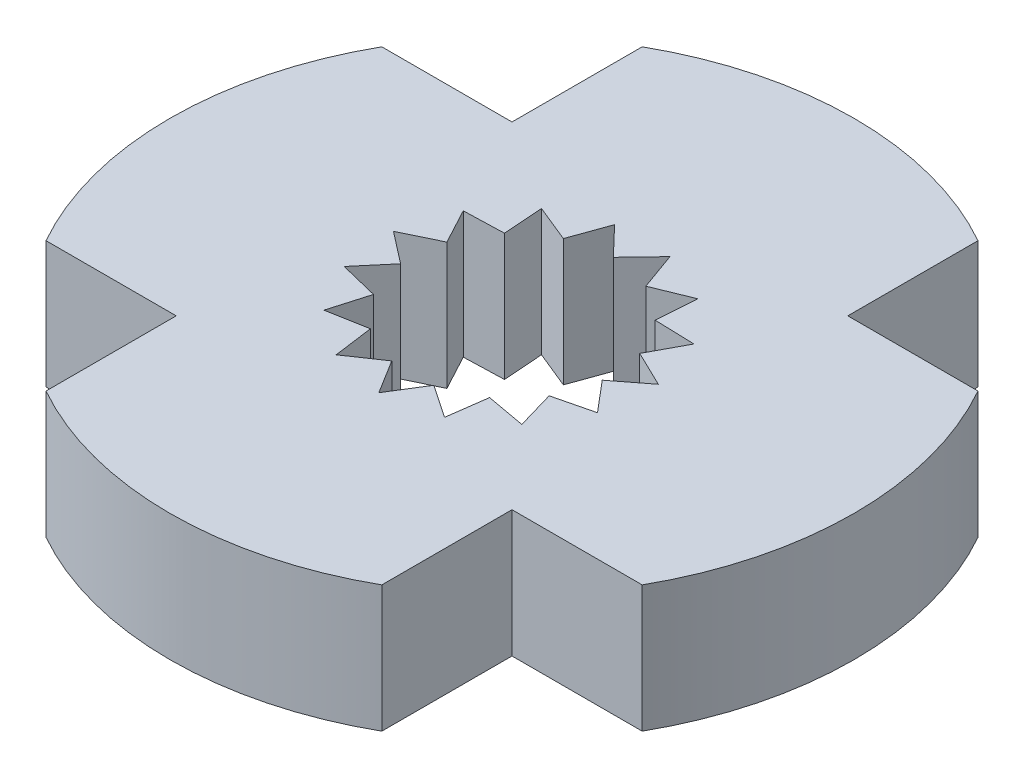
SolidWorks part; units mm, degrees
ref_plane "正面" through (0, 0, 0) normal (0, 0, 1) x (1, 0, 0)
ref_plane "平面" through (0, 0, 0) normal (0, 1, 0) x (1, 0, 0)
ref_plane "右側面" through (0, 0, 0) normal (1, 0, 0) x (0, 0, -1)
sketch "ｽｹｯﾁ1" plane through (0, 0, 0) normal (0, 1, 0) x (1, 0, 0)
  line L30 (0, 1.6) -> (0.437, 2.056) construction
  line L31 (0.6508, 1.4617) -> (1.2355, 1.7005) construction
  line L32 (0.6508, 1.4617) -> (0.437, 2.056) construction
  line L33 (1.189, 1.0706) -> (1.8203, 1.051) construction
  line L34 (1.189, 1.0706) -> (1.2355, 1.7005) construction
  line L35 (1.5217, 0.4944) -> (2.0904, 0.2197) construction
  line L36 (1.5217, 0.4944) -> (1.8203, 1.051) construction
  line L37 (1.5912, -0.1672) -> (1.9991, -0.6495) construction
  line L38 (1.5912, -0.1672) -> (2.0904, 0.2197) construction
  line L39 (1.3856, -0.8) -> (1.562, -1.4065) construction
  line L40 (1.3856, -0.8) -> (1.9991, -0.6495) construction
  line L41 (0.9405, -1.2944) -> (0.8549, -1.9202) construction
  line L42 (0.9405, -1.2944) -> (1.562, -1.4065) construction
  line L43 (0.3327, -1.565) -> (0, -2.1019) construction
  line L44 (0.3327, -1.565) -> (0.8549, -1.9202) construction
  line L45 (-0.3327, -1.565) -> (-0.8549, -1.9202) construction
  line L46 (-0.3327, -1.565) -> (0, -2.1019) construction
  line L47 (-0.9405, -1.2944) -> (-1.562, -1.4065) construction
  line L48 (-0.9405, -1.2944) -> (-0.8549, -1.9202) construction
  line L49 (-1.3856, -0.8) -> (-1.9991, -0.6495) construction
  line L50 (-1.3856, -0.8) -> (-1.562, -1.4065) construction
  line L51 (-1.5912, -0.1672) -> (-2.0904, 0.2197) construction
  line L52 (-1.5912, -0.1672) -> (-1.9991, -0.6495) construction
  line L53 (-1.5217, 0.4944) -> (-1.8203, 1.051) construction
  line L54 (-1.5217, 0.4944) -> (-2.0904, 0.2197) construction
  line L55 (-1.189, 1.0706) -> (-1.2355, 1.7005) construction
  line L56 (-1.189, 1.0706) -> (-1.8203, 1.051) construction
  line L57 (-0.6508, 1.4617) -> (-0.437, 2.056) construction
  line L58 (-0.6508, 1.4617) -> (-1.2355, 1.7005) construction
  line L59 (0, 1.6) -> (-0.437, 2.056) construction
  line L60 (2.65, 4.7051) -> (2.65, 2.65)
  line L61 (-2.65, 4.7051) -> (-2.65, 2.65)
  line L63 (-4.7051, 2.65) -> (-2.65, 2.65)
  line L64 (-4.7051, -2.65) -> (-2.65, -2.65)
  line L65 (-2.65, -2.65) -> (-2.65, -4.7051)
  line L66 (2.65, -2.65) -> (2.65, -4.7051)
  line L67 (2.65, 2.65) -> (4.7051, 2.65)
  line L68 (2.65, -2.65) -> (4.7051, -2.65)
  arc A2 (-4.7051, 2.65) -> (-4.7051, -2.65) centre (0, 0) ccw
  arc A3 (2.65, 4.7051) -> (-2.65, 4.7051) centre (0, 0) ccw
  arc A4 (4.7051, -2.65) -> (4.7051, 2.65) centre (0, 0) ccw
  arc A5 (-2.65, -4.7051) -> (2.65, -4.7051) centre (0, 0) ccw
extrude "ﾎﾞｽ - 押し出し1" add sketch "ｽｹｯﾁ1" along normal blind 2
sketch "ｽｹｯﾁ2" plane through (0, 0, 0) normal (0, -1, 0) x (1, 0, 0)
  circle A0 centre (0, 0) radius 2.575
  circle A1 centre (0, 0) radius 0.85
  dimension "D1" = 5.15
  dimension "D2" = 1.7
extrude "ﾎﾞｽ - 押し出し2" [suppressed] add sketch "ｽｹｯﾁ2" along normal blind 1.5
sketch "ｽｹｯﾁ3" [suppressed] plane through (0, -1.5, 0) normal (0, -1, 0) x (1, 0, 0)
  circle A0 centre (0, 0) radius 1.55
  dimension "D1" = 3.1
extrude "ｶｯﾄ - 押し出し1" [suppressed] cut sketch "ｽｹｯﾁ3" against normal blind 0.3
sketch "ｽｹｯﾁ4" plane through (0, 2, 0) normal (0, 1, 0) x (1, 0, 0)
  line L0 (0, 0) -> (0, 2.4324) construction
  line L1 (0, 0) -> (0.5057, 2.3792) construction
  line L2 (0, 0) -> (0.9893, 2.2221) construction
  line L3 (0, 0) -> (1.4297, 1.9678) construction
  line L4 (0, 0) -> (1.8076, 1.6276) construction
  line L5 (0, 0) -> (2.1065, 1.2162) construction
  line L6 (0, 0) -> (2.3133, 0.7516) construction
  line L7 (0, 0) -> (2.419, 0.2543) construction
  line L24 (0, 0) -> (2.419, -0.2543) construction
  line L25 (0, 0) -> (2.3133, -0.7516) construction
  line L26 (0, 0) -> (2.1065, -1.2162) construction
  line L27 (0, 0) -> (1.8076, -1.6276) construction
  line L28 (0, 0) -> (1.4297, -1.9678) construction
  line L29 (0, 0) -> (0.9893, -2.2221) construction
  line L30 (0, 0) -> (0.5057, -2.3792) construction
  line L31 (0, 0) -> (0, -2.4324) construction
  line L32 (0, 0) -> (-0.5057, -2.3792) construction
  line L33 (0, 0) -> (-0.9893, -2.2221) construction
  line L34 (0, 0) -> (-1.4297, -1.9678) construction
  line L35 (0, 0) -> (-1.8076, -1.6276) construction
  line L36 (0, 0) -> (-2.1065, -1.2162) construction
  line L37 (0, 0) -> (-2.3133, -0.7516) construction
  line L38 (0, 0) -> (-2.419, -0.2543) construction
  line L39 (0, 0) -> (-2.419, 0.2543) construction
  line L40 (0, 0) -> (-2.3133, 0.7516) construction
  line L41 (0, 0) -> (-2.1065, 1.2162) construction
  line L42 (0, 0) -> (-1.8076, 1.6276) construction
  line L43 (0, 0) -> (-1.4297, 1.9678) construction
  line L44 (0, 0) -> (-0.9893, 2.2221) construction
  line L45 (0, 0) -> (-0.5057, 2.3792) construction
  line L46 (0, 1.6) -> (0.437, 2.056)
  line L47 (0.6508, 1.4617) -> (1.2355, 1.7005)
  line L48 (0.6508, 1.4617) -> (0.437, 2.056)
  line L49 (1.189, 1.0706) -> (1.8203, 1.051)
  line L50 (1.189, 1.0706) -> (1.2355, 1.7005)
  line L51 (1.5217, 0.4944) -> (2.0904, 0.2197)
  line L52 (1.5217, 0.4944) -> (1.8203, 1.051)
  line L53 (1.5912, -0.1672) -> (1.9991, -0.6495)
  line L54 (1.5912, -0.1672) -> (2.0904, 0.2197)
  line L55 (1.3856, -0.8) -> (1.562, -1.4065)
  line L56 (1.3856, -0.8) -> (1.9991, -0.6495)
  line L57 (0.9405, -1.2944) -> (0.8549, -1.9202)
  line L58 (0.9405, -1.2944) -> (1.562, -1.4065)
  line L59 (0.3327, -1.565) -> (0, -2.1019)
  line L60 (0.3327, -1.565) -> (0.8549, -1.9202)
  line L61 (-0.3327, -1.565) -> (-0.8549, -1.9202)
  line L62 (-0.3327, -1.565) -> (0, -2.1019)
  line L63 (-0.9405, -1.2944) -> (-1.562, -1.4065)
  line L64 (-0.9405, -1.2944) -> (-0.8549, -1.9202)
  line L65 (-1.3856, -0.8) -> (-1.9991, -0.6495)
  line L66 (-1.3856, -0.8) -> (-1.562, -1.4065)
  line L67 (-1.5912, -0.1672) -> (-2.0904, 0.2197)
  line L68 (-1.5912, -0.1672) -> (-1.9991, -0.6495)
  line L69 (-1.5217, 0.4944) -> (-1.8203, 1.051)
  line L70 (-1.5217, 0.4944) -> (-2.0904, 0.2197)
  line L71 (-1.189, 1.0706) -> (-1.2355, 1.7005)
  line L72 (-1.189, 1.0706) -> (-1.8203, 1.051)
  line L73 (-0.6508, 1.4617) -> (-0.437, 2.056)
  line L74 (-0.6508, 1.4617) -> (-1.2355, 1.7005)
  line L75 (0, 1.6) -> (-0.437, 2.056)
  circle A0 centre (0, 0) radius 1.95 construction
  circle A1 centre (0, 0) radius 1.6 construction
  point P50 (0, 0)
  point P73 (0, 0)
  point P81 (0, 0)
  dimension "D2" = 3.9
  dimension "D3" = 3.2
extrude "ｶｯﾄ - 押し出し2" cut sketch "ｽｹｯﾁ4" against normal blind 2.2
